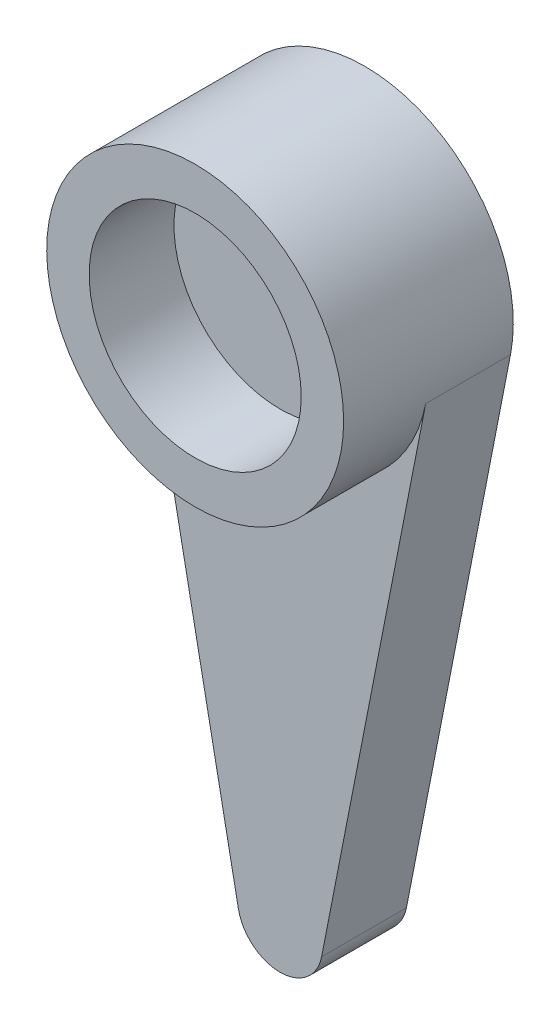
SolidWorks part; units mm, degrees
ref_plane "Front Plane" through (0, 0, 0) normal (0, 0, 1) x (1, 0, 0)
ref_plane "Top Plane" through (0, 0, 0) normal (0, 1, 0) x (1, 0, 0)
ref_plane "Right Plane" through (0, 0, 0) normal (1, 0, 0) x (0, 0, -1)
sketch "Sketch1" plane through (0, 0, 0) normal (0, 0, 1) x (1, 0, 0)
  line L0 (0, 0) -> (0, -13) construction
  line L1 (-0.9813, -13.1923) -> (-3.4347, -0.6731)
  line L2 (0.9813, -13.1923) -> (3.4347, -0.6731)
  arc A0 (3.4347, -0.6731) -> (-3.4347, -0.6731) centre (0, 0) ccw
  arc A1 (-0.9813, -13.1923) -> (0.9813, -13.1923) centre (0, -13) ccw
  point P1 (0, 0)
  point P2 (0, 0)
  point P7 (0, -14)
  point P10 (0, 3.5)
  point P11 (0, 0)
  dimension "D1" = 7
  dimension "D3" = 2
  dimension "D2" = 13
extrude "Boss-Extrude1" add sketch "Sketch1" along normal blind 2 contours A0 L1 A1 L2
sketch "Sketch2" plane through (0, 0, 2) normal (0, 0, 1) x (1, 0, 0)
  circle A0 centre (0, 0) radius 3.5
  arc A1 (3.4347, -0.6731) -> (-3.4347, -0.6731) centre (0, 0) ccw construction
  circle A2 centre (0, 0) radius 2.5
  dimension "D1" = 1
extrude "Boss-Extrude2" add sketch "Sketch2" along normal blind 2
